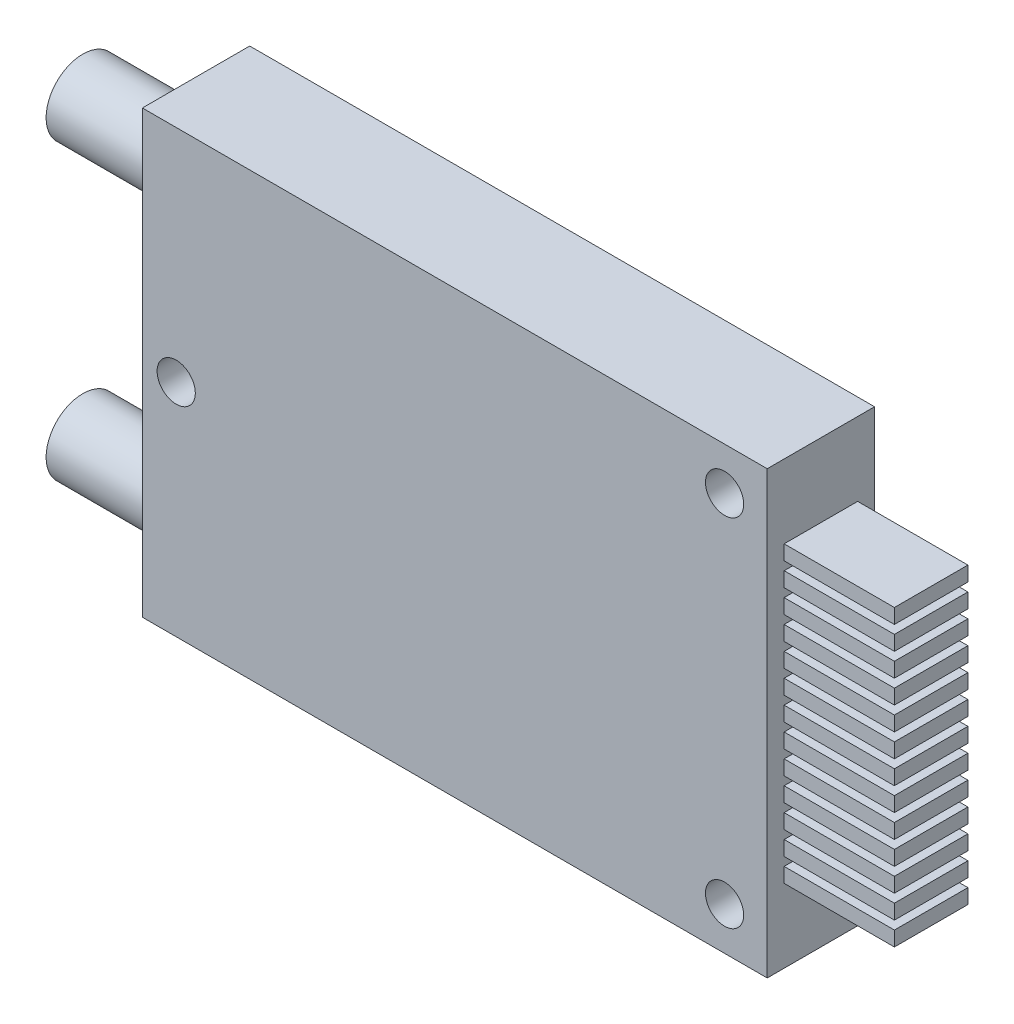
SolidWorks part; units mm, degrees
ref_plane "Front Plane" through (0, 0, 0) normal (0, 0, 1) x (1, 0, 0)
ref_plane "Top Plane" through (0, 0, 0) normal (0, 1, 0) x (1, 0, 0)
ref_plane "Right Plane" through (0, 0, 0) normal (1, 0, 0) x (0, 0, -1)
sketch "Sketch1" plane through (0, 0, 0) normal (0, 0, 1) x (1, 0, 0)
  line L1 (-21.25, 15) -> (21.25, 15)
  line L2 (-21.25, 15) -> (-21.25, -15)
  line L3 (-21.25, -15) -> (21.25, -15)
  line L4 (21.25, 15) -> (21.25, -15)
  point P4 (0, -15)
  point P5 (21.25, 0)
  dimension "D1" = 42.5
  dimension "D2" = 30
extrude "Boss-Extrude1" add sketch "Sketch1" along normal blind 7.3 contours L2 L3 L4 L1
sketch "Sketch2" plane through (0, 0, 7.3) normal (0, 0, 1) x (1, 0, 0)
  line L0 (-21.25, 15) -> (21.25, 15) construction
  line L1 (21.25, 15) -> (21.25, -15) construction
  line L2 (-21.25, -15) -> (21.25, -15) construction
  line L3 (-21.25, 15) -> (-21.25, -15) construction
  circle A0 centre (18.35, -12.1) radius 1.3
  circle A1 centre (18.35, 12.1) radius 1.3
  circle A2 centre (-18.95, 0) radius 1.3
  point P8 (0, 0)
  point P10 (0, 0)
  point P16 (0, 0)
  dimension "D1" = 2.6
  dimension "D2" = 2.9
  dimension "D3" = 2.9
  dimension "D4" = 2.9
  dimension "D5" = 2.9
  dimension "D6" = 2.3
  dimension "D7" = 15
extrude "Cut-Extrude1" cut sketch "Sketch2" against normal up to next
sketch "Sketch3" plane through (-21.25, 0, 0) normal (-1, 0, 0) x (0, 0, 1)
  line L0 (7.3, -15) -> (0, -15) construction
  line L1 (7.3, 15) -> (0, 15) construction
  circle A0 centre (3.65, 10) radius 2.5
  circle A1 centre (3.65, -10) radius 2.5
  point P4 (0, 0)
  point P5 (0, 0)
  point P8 (3.65, -15)
  dimension "D1" = 5
  dimension "D2" = 5
  dimension "D3" = 5
extrude "Boss-Extrude2" add sketch "Sketch3" along normal blind 7.7
sketch "Sketch4" plane through (21.25, 0, 0) normal (1, 0, 0) x (0, 0, -1)
  line L1 (-6.15, 10) -> (-1.15, 10)
  line L2 (-6.15, 10) -> (-6.15, 9)
  line L3 (-6.15, 9) -> (-1.15, 9)
  line L4 (-1.15, 10) -> (-1.15, 9)
  line L9 (-7.3, 15) -> (0, 15) construction
  line L10 (-6.15, 8.4167) -> (-1.15, 8.4167)
  line L11 (-6.15, 8.4167) -> (-6.15, 7.4167)
  line L12 (-6.15, 7.4167) -> (-1.15, 7.4167)
  line L13 (-1.15, 8.4167) -> (-1.15, 7.4167)
  line L14 (-6.15, 6.8333) -> (-1.15, 6.8333)
  line L15 (-6.15, 6.8333) -> (-6.15, 5.8333)
  line L16 (-6.15, 5.8333) -> (-1.15, 5.8333)
  line L17 (-1.15, 6.8333) -> (-1.15, 5.8333)
  line L18 (-6.15, 5.25) -> (-1.15, 5.25)
  line L19 (-6.15, 5.25) -> (-6.15, 4.25)
  line L20 (-6.15, 4.25) -> (-1.15, 4.25)
  line L21 (-1.15, 5.25) -> (-1.15, 4.25)
  line L22 (-6.15, 3.6667) -> (-1.15, 3.6667)
  line L23 (-6.15, 3.6667) -> (-6.15, 2.6667)
  line L24 (-6.15, 2.6667) -> (-1.15, 2.6667)
  line L25 (-1.15, 3.6667) -> (-1.15, 2.6667)
  line L26 (-6.15, 2.0833) -> (-1.15, 2.0833)
  line L27 (-6.15, 2.0833) -> (-6.15, 1.0833)
  line L28 (-6.15, 1.0833) -> (-1.15, 1.0833)
  line L29 (-1.15, 2.0833) -> (-1.15, 1.0833)
  line L30 (-6.15, 0.5) -> (-1.15, 0.5)
  line L31 (-6.15, 0.5) -> (-6.15, -0.5)
  line L32 (-6.15, -0.5) -> (-1.15, -0.5)
  line L33 (-1.15, 0.5) -> (-1.15, -0.5)
  line L34 (-6.15, -1.0833) -> (-1.15, -1.0833)
  line L35 (-6.15, -1.0833) -> (-6.15, -2.0833)
  line L36 (-6.15, -2.0833) -> (-1.15, -2.0833)
  line L37 (-1.15, -1.0833) -> (-1.15, -2.0833)
  line L38 (-6.15, -2.6667) -> (-1.15, -2.6667)
  line L39 (-6.15, -2.6667) -> (-6.15, -3.6667)
  line L40 (-6.15, -3.6667) -> (-1.15, -3.6667)
  line L41 (-1.15, -2.6667) -> (-1.15, -3.6667)
  line L42 (-6.15, -4.25) -> (-1.15, -4.25)
  line L43 (-6.15, -4.25) -> (-6.15, -5.25)
  line L44 (-6.15, -5.25) -> (-1.15, -5.25)
  line L45 (-1.15, -4.25) -> (-1.15, -5.25)
  line L46 (-6.15, -5.8333) -> (-1.15, -5.8333)
  line L47 (-6.15, -5.8333) -> (-6.15, -6.8333)
  line L48 (-6.15, -6.8333) -> (-1.15, -6.8333)
  line L49 (-1.15, -5.8333) -> (-1.15, -6.8333)
  line L50 (-6.15, -7.4167) -> (-1.15, -7.4167)
  line L51 (-6.15, -7.4167) -> (-6.15, -8.4167)
  line L52 (-6.15, -8.4167) -> (-1.15, -8.4167)
  line L53 (-1.15, -7.4167) -> (-1.15, -8.4167)
  line L54 (-6.15, -9) -> (-1.15, -9)
  line L55 (-6.15, -9) -> (-6.15, -10)
  line L56 (-6.15, -10) -> (-1.15, -10)
  line L57 (-1.15, -9) -> (-1.15, -10)
  line L58 (-7.3, -15) -> (0, -15) construction
  point P6 (-3.65, 15)
  point P9 (-3.65, 10)
  dimension "D1" = 5
  dimension "D2" = 1
  dimension "D3" = 5
  dimension "D5" = 5
  dimension "D4" = 13
extrude "Boss-Extrude3" add sketch "Sketch4" along normal blind 7.5
